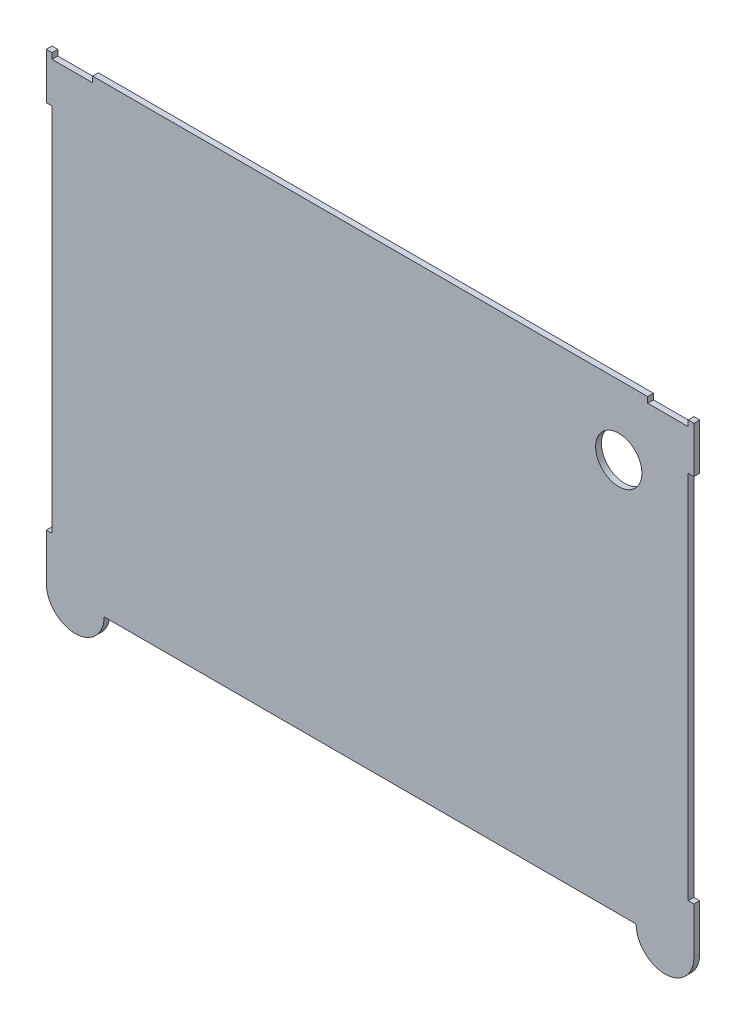
SolidWorks part; units mm, degrees
ref_plane "Front Plane" through (0, 0, 0) normal (0, 0, 1) x (1, 0, 0)
ref_plane "Top Plane" through (0, 0, 0) normal (0, 1, 0) x (1, 0, 0)
ref_plane "Right Plane" through (0, 0, 0) normal (1, 0, 0) x (0, 0, -1)
sketch "Sketch1" plane through (0, 0, 0) normal (0, 0, 1) x (1, 0, 0)
  line L0 (0, 228.6) -> (0, 250.825)
  line L1 (31.75, 0) -> (323.85, 0)
  line L2 (0, 0) -> (0, 25.4)
  line L3 (3.175, 250.825) -> (25.4, 250.825)
  line L4 (355.6, 0) -> (355.6, 25.4)
  line L5 (0, 228.6) -> (3.175, 228.6)
  line L7 (0, 25.4) -> (3.175, 25.4)
  line L8 (3.175, 228.6) -> (3.175, 25.4)
  line L9 (355.6, 228.6) -> (352.425, 228.6)
  line L11 (355.6, 25.4) -> (352.425, 25.4)
  line L12 (352.425, 228.6) -> (352.425, 25.4)
  line L17 (355.6, 228.6) -> (355.6, 250.825)
  line L18 (330.2, 250.825) -> (352.425, 250.825)
  line L19 (0, 250.825) -> (0, 254)
  line L20 (0, 254) -> (3.175, 254)
  line L21 (25.4, 250.825) -> (25.4, 254)
  line L22 (25.4, 254) -> (330.2, 254)
  line L23 (330.2, 254) -> (330.2, 250.825)
  line L24 (3.175, 254) -> (3.175, 250.825)
  line L25 (355.6, 250.825) -> (355.6, 254)
  line L26 (355.6, 254) -> (352.425, 254)
  line L27 (352.425, 254) -> (352.425, 250.825)
  arc A0 (0, 0) -> (31.75, 0) centre (15.875, 0) ccw
  arc A1 (355.6, 0) -> (323.85, 0) centre (339.725, 0) cw
  dimension "D12" = 15.875
  dimension "D1" = 250.825
  dimension "D2" = 355.6
  dimension "D4" = 3.175
  dimension "D5" = 3.175
  dimension "D6" = 203.2
  dimension "D8" = 203.2
  dimension "D9" = 25.4
  dimension "D10" = 25.4
  dimension "D13" = 3.175
extrude "Boss-Extrude1" add sketch "Sketch1" along normal blind 3.175
sketch "Sketch2" plane through (0, 0, 3.175) normal (0, 0, 1) x (1, 0, 0)
  line L0 (330.2, 254) -> (25.4, 254) construction
  line L1 (352.425, 25.4) -> (352.425, 228.6) construction
  circle A0 centre (314.325, 215.9) radius 12.7
  point P2 (0, 0)
  dimension "D1" = 25.4
  dimension "D2" = 38.1
  dimension "D3" = 38.1
extrude "Cut-Extrude1" cut sketch "Sketch2" against normal through all
